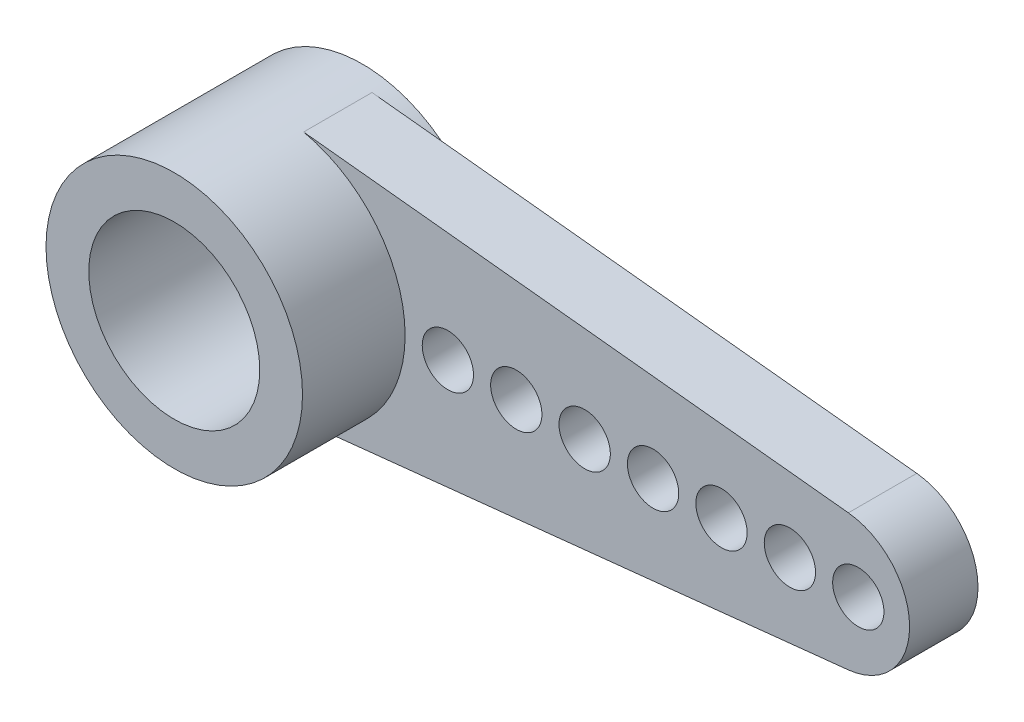
SolidWorks part; units mm, degrees
ref_plane "Спереди" through (0, 0, 0) normal (0, 0, 1) x (1, 0, 0)
ref_plane "Сверху" through (0, 0, 0) normal (0, 1, 0) x (1, 0, 0)
ref_plane "Справа" through (0, 0, 0) normal (1, 0, 0) x (0, 0, -1)
sketch "Эскиз1" plane through (0, 0, 0) normal (0, 0, 1) x (1, 0, 0)
  line L0 (0, 0) -> (-16.5, 0)
  line L1 (-16.7096, 1.989) -> (0, 3.75)
  line L2 (-16.7096, -1.989) -> (0, -3.75)
  line L4 (16.7096, -1.989) -> (0, -3.75)
  line L5 (16.7096, 1.989) -> (0, 3.75)
  circle A0 centre (0, 0) radius 3.75
  circle A1 centre (0, 0) radius 2.5
  arc A2 (-16.467, -1.9997) -> (-16.7096, 1.989) centre (-16.5, 0) cw
  arc A3 (16.7096, -1.989) -> (16.7096, 1.989) centre (16.5, 0) ccw
  dimension "D1" = 7.5
  dimension "D2" = 5
  dimension "D4" = 2
  dimension "D3" = 16.5
extrude "Бобышка-Вытянуть3" add sketch "Эскиз1" along normal blind 2
sketch "Эскиз2" plane through (0, 0, 2) normal (0, 0, 1) x (1, 0, 0)
  circle A0 centre (0, 0) radius 3.75
  circle A1 centre (0, 0) radius 2.5
  dimension "D1" = 5
extrude "Бобышка-Вытянуть5" add sketch "Эскиз2" along normal blind 3 separate body
sketch "Эскиз3" plane through (0, 0, 2) normal (0, 0, -1) x (-1, 0, 0)
  circle A0 centre (0, 0) radius 3.75
  circle A1 centre (0, 0) radius 2.5
  circle A2 centre (0, 0) radius 3.75 construction
extrude "Бобышка-Вытянуть6" add sketch "Эскиз3" along normal offset from surface (2.5 mm away) 0.5 up to face at (9.9353, 0, 0) offset beyond the face yes
sketch "Эскиз4" plane through (0, 0, 0) normal (0, 0, -1) x (-1, 0, 0)
  line L0 (-18.5, 0) -> (-17, 0)
  line L1 (-17, 0) -> (-15, 0)
  line L2 (-15, 0) -> (-13, 0)
  line L3 (-13, 0) -> (-11, 0)
  line L4 (-11, 0) -> (-9, 0)
  line L5 (-9, 0) -> (-7, 0)
  arc A0 (-16.7096, 1.989) -> (-16.7096, -1.989) centre (-16.5, 0) ccw construction
  circle A1 centre (-17, 0) radius 0.75
  circle A2 centre (-15, 0) radius 0.75
  circle A3 centre (-13, 0) radius 0.75
  circle A4 centre (-11, 0) radius 0.75
  circle A5 centre (-9, 0) radius 0.75
  circle A6 centre (-7, 0) radius 0.75
  circle A7 centre (4.5, 0) radius 0.5
  circle A8 centre (6.5, 0) radius 0.5
  circle A9 centre (8.5, 0) radius 0.5
  circle A10 centre (10.5, 0) radius 0.5
  circle A11 centre (12.5, 0) radius 0.5
  circle A12 centre (14.5, 0) radius 0.5
  circle A13 centre (-5, 0) radius 0.75
  dimension "D2" = 2
  dimension "D12" = 1.5
  dimension "D1" = 1.5
  dimension "D3" = 2
  dimension "D4" = 2
  dimension "D5" = 2
  dimension "D6" = 2
  dimension "D7" = 2
extrude "Вырез-Вытянуть1" cut sketch "Эскиз4" against normal blind 2
sketch "Эскиз5" plane through (0, 0, 0) normal (0, 0, -1) x (-1, 0, 0)
  circle A0 centre (0, 0) radius 2.5
extrude "Бобышка-Вытянуть7" add sketch "Эскиз5" against normal blind 1
sketch "Эскиз6" plane through (0, 0, 0) normal (0, 0, -1) x (-1, 0, 0)
  circle A0 centre (0, 0) radius 2.5
  dimension "D1" = 5
extrude "Вырез-Вытянуть2" cut sketch "Эскиз6" against normal blind 0.5
sketch "Эскиз7" plane through (0, 0, 0.5) normal (0, 0, -1) x (-1, 0, 0)
  circle A0 centre (0, 0) radius 1.25
  dimension "D1" = 2.5
extrude "Вырез-Вытянуть3" cut sketch "Эскиз7" against normal blind 5
ref_plane "Plane1" through (0, 0, 5.65) normal (0, 0, -1) x (-1, 0, 0)
